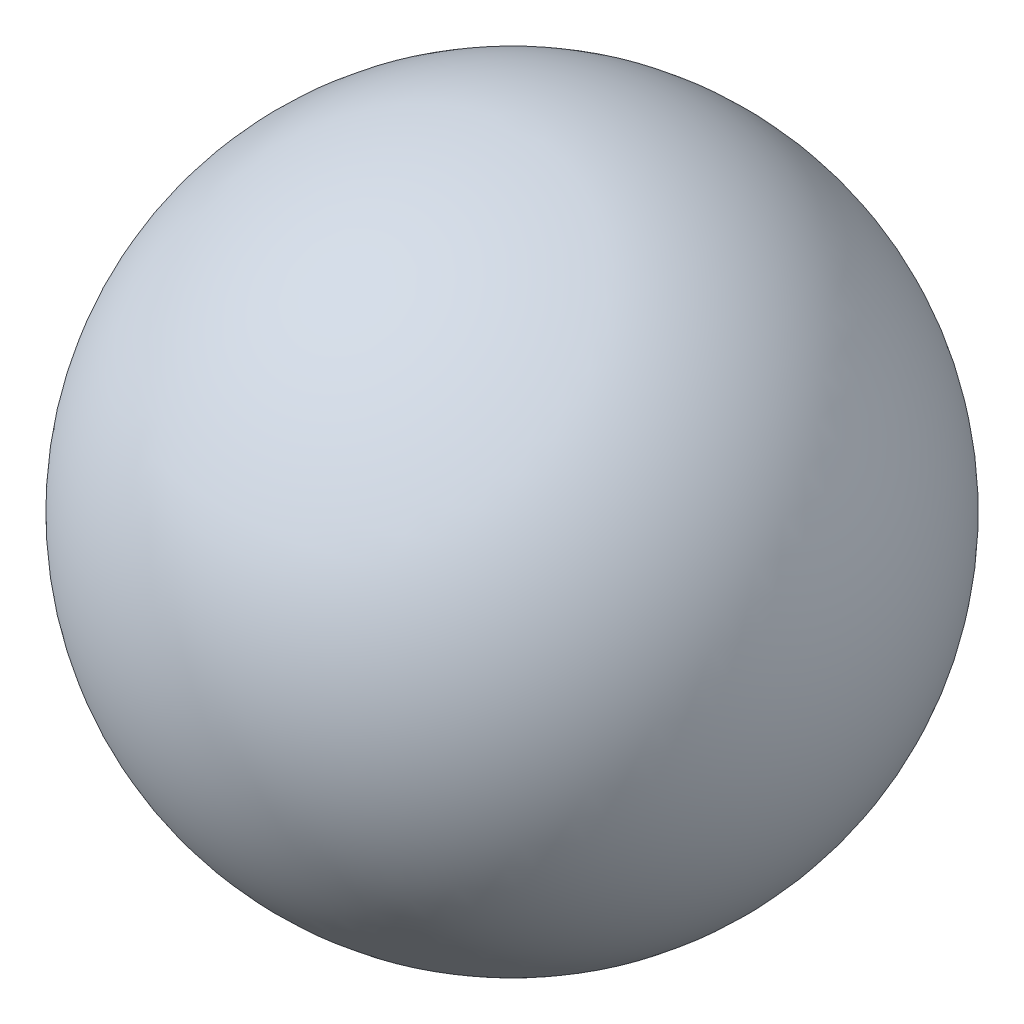
SolidWorks part; units mm, degrees
ref_plane "Front Plane" through (0, 0, 0) normal (0, 0, 1) x (1, 0, 0)
ref_plane "Top Plane" through (0, 0, 0) normal (0, 1, 0) x (1, 0, 0)
ref_plane "Right Plane" through (0, 0, 0) normal (1, 0, 0) x (0, 0, -1)
sketch "Sketch1" plane through (0, 0, 0) normal (0, 0, 1) x (1, 0, 0)
  line L0 (0, 100) -> (0, -100)
  arc A0 (0, 100) -> (0, -100) centre (0, 0) ccw
  dimension "D1" = 100
revolve "Revolve1" add sketch "Sketch1" angle 360 about L0
